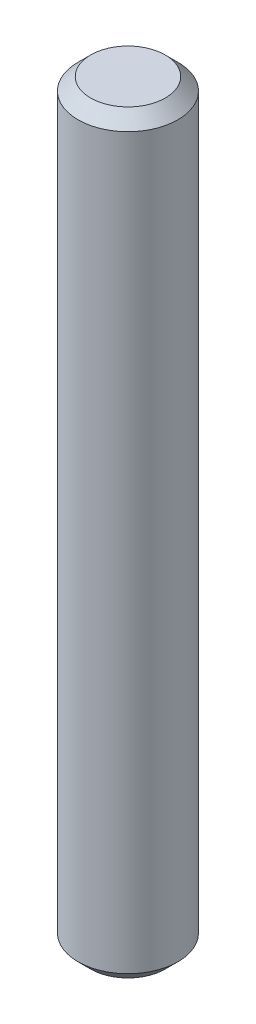
SolidWorks part; units mm, degrees
ref_plane "Front Plane" through (0, 0, 0) normal (0, 0, 1) x (1, 0, 0)
ref_plane "Top Plane" through (0, 0, 0) normal (0, 1, 0) x (1, 0, 0)
ref_plane "Right Plane" through (0, 0, 0) normal (1, 0, 0) x (0, 0, -1)
sketch "Sketch1" plane through (0, 0, 0) normal (0, 1, 0) x (1, 0, 0)
  circle A0 centre (0, 0) radius 3.9688
  dimension "D1" = 7.9375
extrude "Boss-Extrude1" add sketch "Sketch1" along normal blind 60 contours A0
cosmetic thread "Cosmetic Thread4" parameters "D2"=6.619
chamfer "Chamfer1" distance 1 angle 45 2 edges at (0, 0, 3.9688) (0, 60, 3.9688)
